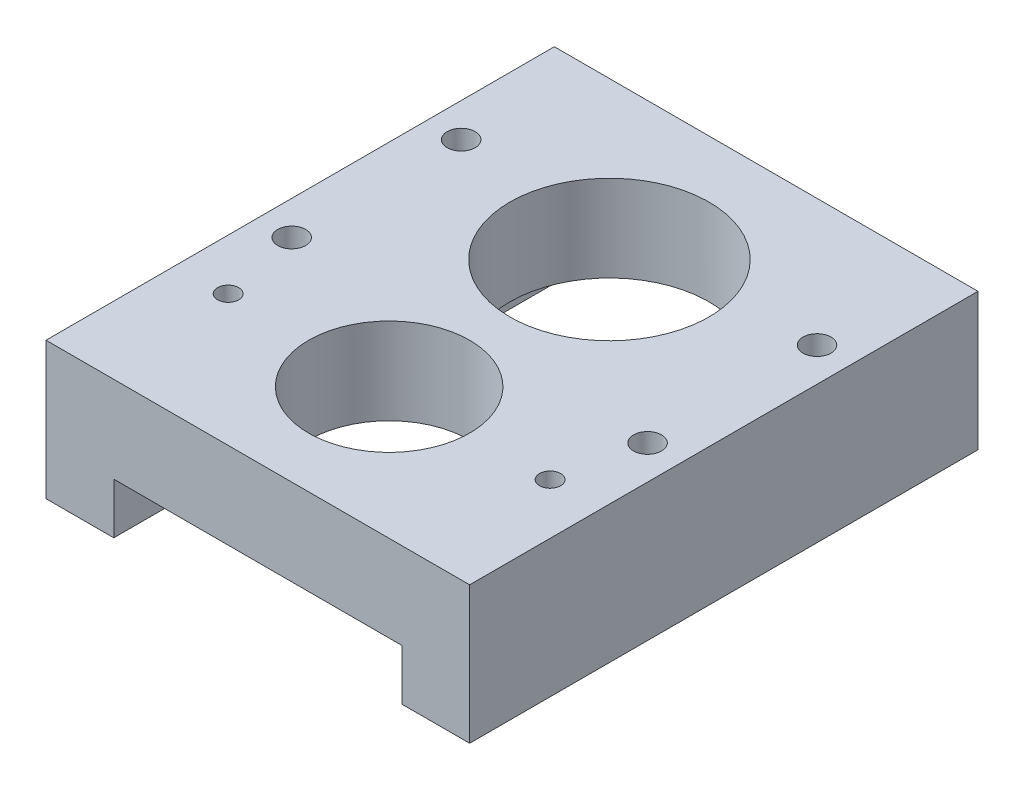
SolidWorks part; units mm, degrees
material "6061 合金"
ref_plane "前基準面" through (0, 0, 0) normal (0, 0, 1) x (1, 0, 0)
ref_plane "上基準面" through (0, 0, 0) normal (0, 1, 0) x (1, 0, 0)
ref_plane "右基準面" through (0, 0, 0) normal (1, 0, 0) x (0, 0, -1)
sketch "草圖1" plane through (0, 0, 0) normal (0, 0, 1) x (1, 0, 0)
  line L0 (-25, 0) -> (-17, 0)
  line L1 (-17, 0) -> (-17, 6)
  line L2 (-17, 6) -> (17, 6)
  line L3 (17, 6) -> (17, 0)
  line L4 (17, 0) -> (25, 0)
  line L5 (25, 0) -> (25, 16.2)
  line L6 (25, 16.2) -> (-25, 16.2)
  line L7 (-25, 16.2) -> (-25, 0)
  point P3 (0, 6)
  dimension "D1" = 6
  dimension "D2" = 16.2
  dimension "D3" = 8
  dimension "D4" = 50
extrude "填料-伸長1" add sketch "草圖1" along normal blind 60
sketch "草圖2" plane through (0, 16.2, 0) normal (0, 1, 0) x (1, 0, 0)
  line L0 (25, 0) -> (-25, 0) construction
  circle A0 centre (0, -18.5) radius 11.75
  point P5 (0, 0)
  dimension "D2" = 23.5
  dimension "D1" = 18.5
extrude "除料-伸長1" cut sketch "草圖2" against normal blind 40
sketch "草圖3" plane through (0, 16.2, 0) normal (0, 1, 0) x (1, 0, 0)
  line L0 (25, 0) -> (-25, 0) construction
  circle A0 centre (0, -44.5) radius 9.5
  circle A1 centre (0, -18.5) radius 11.75 construction
  point P7 (0, 0)
  dimension "D1" = 26
  dimension "D2" = 19
extrude "除料-伸長2" cut sketch "草圖3" against normal blind 40
hole_wizard "M3x0.5 螺紋孔1" positions "草圖5" profile "草圖6" tap size "M3x0.5" standard "Ansi Metric"
sketch "草圖5" plane through (0, 16.2, 0) normal (0, 1, 0) x (1, 0, 0)
  line L0 (25, -60) -> (25, 0) construction
  line L1 (25, -60) -> (-25, -60) construction
  line L2 (-25, -60) -> (-25, 0) construction
  point P0 (19, -44.5)
  point P3 (-19, -44.5)
  dimension "D1" = 6
  dimension "D2" = 15.5
  dimension "D3" = 6
  dimension "D4" = 15.5
sketch "草圖6" plane through (19, 16.2, 44.5) normal (1, 0, 0) x (0, 0, 1)
  line L0 (0, 0) -> (0, 5.7511)
  line L1 (0, 5.7511) -> (1.25, 5)
  line L2 (1.25, 5) -> (1.25, 0)
  line L5 (1.25, 0) -> (0, 0)
  line L10 (0, 5.7511) -> (-1.25, 5) construction
  line L11 (0, -6.35) -> (0, 107.95) construction
  dimension "螺孔鑽直徑" = 2.5
  dimension "螺孔鑽深度" = 5
  dimension "導頭角度" = 118
cosmetic thread "鑽孔螺紋1" parameters "D1"=6, "D2"=3
cosmetic thread "鑽孔螺紋2" parameters "D1"=6, "D2"=3
sketch "草圖7" plane through (0, 16.2, 0) normal (0, 1, 0) x (1, 0, 0)
  line L0 (25, 0) -> (-25, 0) construction
  line L1 (21, -35) -> (-21, -35) construction
  line L2 (21, -35) -> (21, -15) construction
  line L3 (21, -15) -> (-21, -15) construction
  line L4 (-21, -35) -> (-21, -15) construction
  circle A0 centre (-21, -35) radius 1.65
  circle A1 centre (-21, -15) radius 1.65
  circle A2 centre (21, -35) radius 1.65
  circle A3 centre (21, -15) radius 1.65
  point P8 (0, -35)
  point P11 (0, 0)
  dimension "D1" = 3.3
  dimension "D2" = 3.3
  dimension "D3" = 3.3
  dimension "D4" = 3.3
  dimension "D5" = 20
  dimension "D6" = 42
  dimension "D7" = 15
extrude "除料-伸長3" cut sketch "草圖7" against normal up to next
